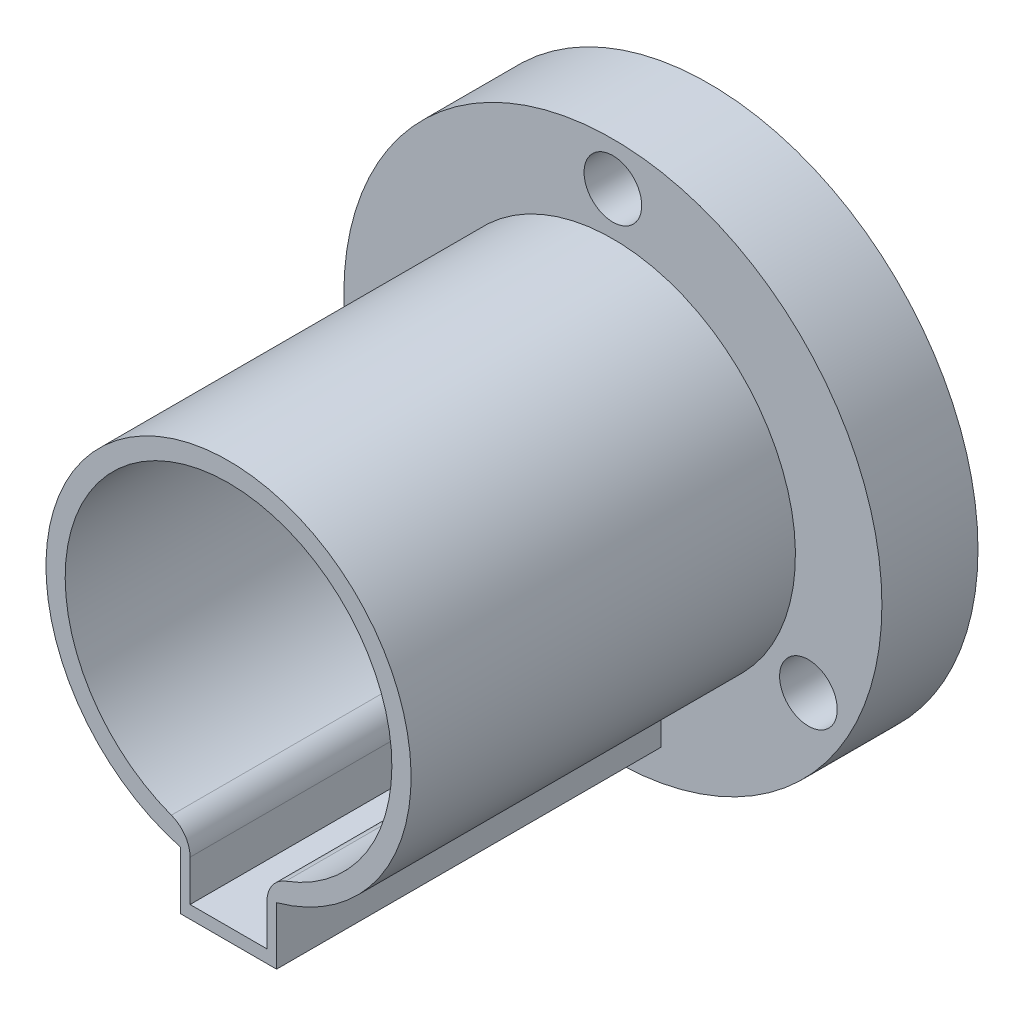
SolidWorks part; units mm, degrees
material "Stainless Steel (ferritic)"
ref_plane "Front Plane" through (0, 0, 0) normal (0, 0, 1) x (1, 0, 0)
ref_plane "Top Plane" through (0, 0, 0) normal (0, 1, 0) x (1, 0, 0)
ref_plane "Right Plane" through (0, 0, 0) normal (1, 0, 0) x (0, 0, -1)
sketch "Sketch1" plane through (0, 0, 0) normal (0, 0, 1) x (1, 0, 0)
  circle A0 centre (0, 0) radius 14
  dimension "D1" = 28
extrude "Boss-Extrude1" add sketch "Sketch1" along normal blind 5
sketch "Sketch2" plane through (0, 0, 5) normal (0, 0, 1) x (1, 0, 0)
  line L2 (2.5, -9.1652) -> (2.5, -12.1652)
  line L3 (2.5, -12.1652) -> (-2.5, -12.1652)
  line L4 (-2.5, -9.1652) -> (-2.5, -12.1652)
  arc A0 (2.5, -9.1652) -> (-2.5, -9.1652) centre (0, 0) ccw
  point P1 (2.8403, -9.0655)
  point P6 (0, -12.1652)
  dimension "D1" = 19
  dimension "D2" = 3
  dimension "D3" = 5
extrude "Boss-Extrude3" add sketch "Sketch2" along normal blind 20
sketch "Sketch3" plane through (0, 0, 25) normal (0, 0, 1) x (1, 0, 0)
  circle A0 centre (0, 0) radius 8.5
  dimension "D1" = 17
extrude "Cut-Extrude1" cut sketch "Sketch3" against normal through all
sketch "Sketch5" plane through (0, 0, 25) normal (0, 0, 1) x (1, 0, 0)
  line L1 (-2, 0) -> (2, 0)
  line L2 (-2, 0) -> (-2, -11.5)
  line L3 (-2, -11.5) -> (2, -11.5)
  line L4 (2, 0) -> (2, -11.5)
  point P4 (0, 0)
  dimension "D1" = 11.5
  dimension "D2" = 4
extrude "Cut-Extrude3" cut sketch "Sketch5" against normal through all
sketch "Sketch6" plane through (0, 0, 5) normal (0, 0, 1) x (1, 0, 0)
  line L0 (0, 9.5) -> (0, 11.75) construction
  line L1 (0, 11.75) -> (0, 14) construction
  circle A0 centre (0, 11.75) radius 1.5
  arc A1 (2.5, -9.1652) -> (-2.5, -9.1652) centre (0, 0) ccw construction
  circle A2 centre (0, 0) radius 14 construction
  dimension "D1" = 3
extrude "Cut-Extrude4" cut sketch "Sketch6" against normal through all
pattern_circular "CirPattern1" count 3 over 360 about axis through (0, 0, 0) along (0, 0, 1) of "Cut-Extrude4"
fillet "Fillet1" radius 1.5 2 edges at (2, -8.2614, 12.5) (-2, -8.2614, 12.5)
